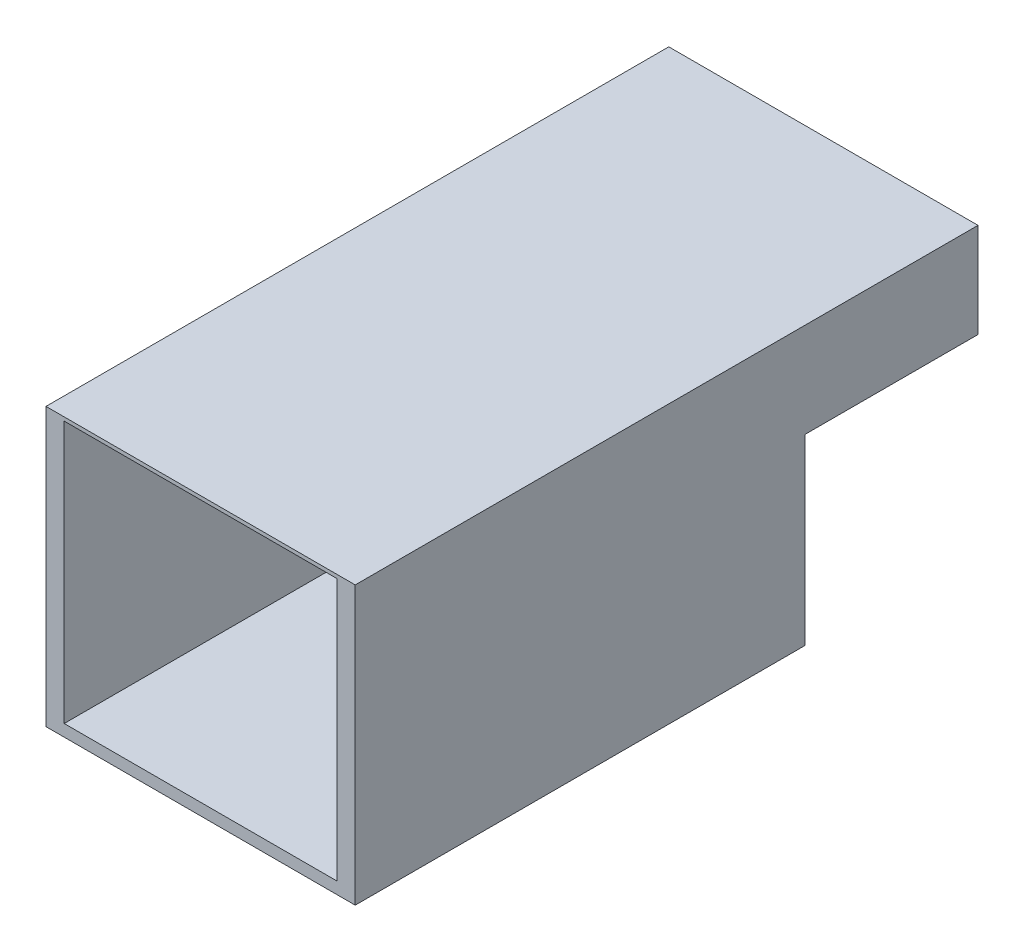
SolidWorks part; units mm, degrees
ref_plane "Front Plane" through (0, 0, 0) normal (0, 0, 1) x (1, 0, 0)
ref_plane "Top Plane" through (0, 0, 0) normal (0, 1, 0) x (1, 0, 0)
ref_plane "Right Plane" through (0, 0, 0) normal (1, 0, 0) x (0, 0, -1)
sketch "Sketch1" plane through (0, 0, 0) normal (1, 0, 0) x (0, 0, -1)
  line L0 (412.496, 387.35) -> (869.696, 387.35)
  line L1 (0, 0) -> (412.496, 0)
  line L2 (0, 0) -> (0, 387.35)
  line L3 (0, 387.35) -> (412.496, 387.35)
  line L4 (412.496, 0) -> (412.496, 387.35) construction
  line L5 (869.696, 387.35) -> (869.696, 255.27)
  line L6 (869.696, 255.27) -> (628.396, 255.27)
  line L7 (628.396, 255.27) -> (628.396, 0)
  line L8 (628.396, 0) -> (412.496, 0)
  line L9 (628.396, 255.27) -> (412.496, 255.27) construction
extrude "Boss-Extrude1" add sketch "Sketch1" along normal blind 431.8
sketch "Sketch2" plane through (0, 0, -628.396) normal (0, 0, -1) x (-1, 0, 0)
  line L1 (-406.4, 247.65) -> (-25.4, 247.65)
  line L2 (-406.4, 247.65) -> (-406.4, 16.51)
  line L3 (-406.4, 16.51) -> (-25.4, 16.51)
  line L4 (-25.4, 247.65) -> (-25.4, 16.51)
extrude "Cut-Extrude1" cut sketch "Sketch2" against normal blind 203.2
sketch "Sketch3" plane through (0, 0, 0) normal (0, 0, 1) x (1, 0, 0)
  line L1 (25.4, 382.27) -> (406.4, 382.27)
  line L2 (25.4, 382.27) -> (25.4, 16.51)
  line L3 (25.4, 16.51) -> (406.4, 16.51)
  line L4 (406.4, 382.27) -> (406.4, 16.51)
extrude "Cut-Extrude2" cut sketch "Sketch3" against normal blind 412.496
